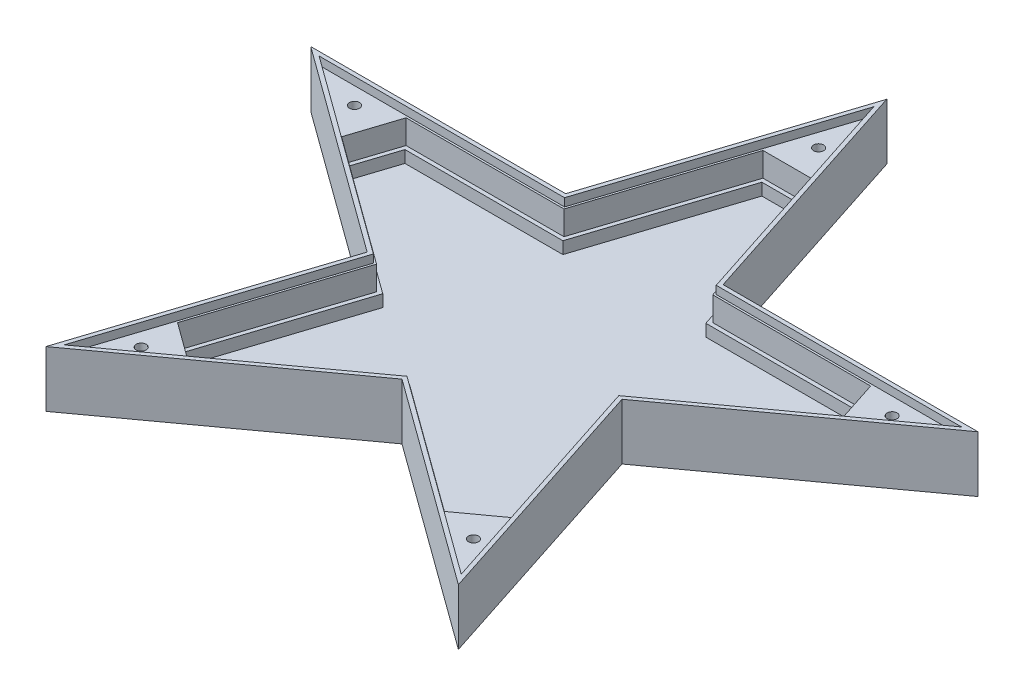
SolidWorks part; units mm, degrees
ref_plane "Alzado" through (0, 0, 0) normal (0, 0, 1) x (1, 0, 0)
ref_plane "Planta" through (0, 0, 0) normal (0, 1, 0) x (1, 0, 0)
ref_plane "Vista lateral" through (0, 0, 0) normal (1, 0, 0) x (0, 0, -1)
sketch "Croquis1" plane through (0, 0, 0) normal (0, 1, 0) x (1, 0, 0)
  line L0 (0, 0) -> (0, 87.5) construction
  line L1 (0, 87.5) -> (-19.645, 27.039)
  line L2 (-19.645, 27.039) -> (-83.2174, 27.039)
  line L3 (-83.2174, 27.039) -> (-31.7862, -10.328)
  line L4 (-31.7862, -10.328) -> (-51.4312, -70.789)
  line L5 (-51.4312, -70.789) -> (0, -33.422)
  line L6 (0, 87.5) -> (-51.4312, -70.789) construction
  line L7 (0, -33.422) -> (0, 0) construction
  line L8 (0, 87.5) -> (19.645, 27.039)
  line L9 (19.645, 27.039) -> (83.2174, 27.039)
  line L10 (83.2174, 27.039) -> (31.7862, -10.328)
  line L11 (31.7862, -10.328) -> (51.4312, -70.789)
  line L12 (51.4312, -70.789) -> (0, -33.422)
  line L14 (0, 87.5) -> (0, 0) construction
  line L15 (0, 0) -> (-83.2174, 27.039) construction
  line L16 (0, 0) -> (83.2174, 27.039) construction
  line L17 (51.4312, -70.789) -> (0, 0) construction
  line L18 (0, 0) -> (-51.4312, -70.789) construction
  line L19 (-55.5183, 23.2963) -> (-7.9655, 7.8455) construction
  line L20 (-7.9655, 7.8455) -> (-11.0557, -1.6651) construction
  line L21 (-11.0557, -1.6651) -> (-58.6085, 13.7857) construction
  line L22 (-58.6085, 13.7857) -> (-55.5183, 23.2963) construction
  line L23 (-39.3122, -45.6021) -> (-9.9229, -5.1512) construction
  line L24 (-9.9229, -5.1512) -> (-1.8328, -11.0291) construction
  line L25 (-1.8328, -11.0291) -> (-31.222, -51.4799) construction
  line L26 (-31.222, -51.4799) -> (-39.3122, -45.6021) construction
  line L27 (-17.8286, 24.539) -> (-75.5232, 24.539) construction
  line L28 (-75.5232, 24.539) -> (-28.8473, -9.3731) construction
  line L29 (-28.8473, -9.3731) -> (-46.6759, -64.2439) construction
  line L30 (-46.6759, -64.2439) -> (0, -30.3319) construction
  line L31 (46.6759, -64.2439) -> (0, -30.3319) construction
  line L32 (28.8473, -9.3731) -> (46.6759, -64.2439) construction
  line L33 (75.5232, 24.539) -> (28.8473, -9.3731) construction
  line L34 (17.8286, 24.539) -> (75.5232, 24.539) construction
  line L35 (0, 79.4098) -> (17.8286, 24.539) construction
  line L36 (0, 79.4098) -> (-17.8286, 24.539) construction
  line L37 (51.4312, -70.789) -> (83.2174, 27.039) construction
  line L38 (0, 87.5) -> (83.2174, 27.039) construction
  line L39 (0, 87.5) -> (-83.2174, 27.039) construction
  line L40 (-83.2174, 27.039) -> (-51.4312, -70.789) construction
  line L41 (-51.4312, -70.789) -> (51.4312, -70.789) construction
  line L42 (5, 60) -> (5, 10) construction
  line L43 (5, 10) -> (-5, 10) construction
  line L44 (-5, 10) -> (-5, 60) construction
  line L45 (-5, 60) -> (5, 60) construction
  line L46 (58.6085, 13.7857) -> (55.5183, 23.2963) construction
  line L47 (55.5183, 23.2963) -> (7.9655, 7.8455) construction
  line L48 (7.9655, 7.8455) -> (11.0557, -1.6651) construction
  line L49 (11.0557, -1.6651) -> (58.6085, 13.7857) construction
  line L50 (31.222, -51.4799) -> (39.3122, -45.6021) construction
  line L51 (39.3122, -45.6021) -> (9.9229, -5.1512) construction
  line L52 (9.9229, -5.1512) -> (1.8328, -11.0291) construction
  line L53 (1.8328, -11.0291) -> (31.222, -51.4799) construction
  circle A0 centre (0, 0) radius 87.5 construction
  circle A1 centre (0, 0) radius 10 construction
  circle A2 centre (0, 0) radius 7.5 construction
  point P15 (-9.5106, 3.0902)
  point P20 (-5.8779, -8.0902)
  point P39 (0, 60)
  dimension "D1" = 175
  dimension "D5" = 20
  dimension "D6" = 15
  dimension "D2" = 50
  dimension "D3" = 10
  dimension "D4" = 2.5
extrude "Saliente-Extruir1" add sketch "Croquis1" along normal blind 14
sketch "Croquis2" plane through (0, 14, 0) normal (0, 1, 0) x (1, 0, 0)
  line L0 (0, -96.25) -> (0, 96.25) construction
  line L1 (31.8662, -53.484) -> (41.0191, -46.8341)
  line L2 (60.7136, 13.7791) -> (57.2175, 24.539)
  line L10 (-60.7136, 13.7791) -> (-57.2175, 24.539)
  line L11 (-58.6085, 13.7857) -> (-55.5183, 23.2963) construction
  line L12 (-31.8662, -53.484) -> (-41.0191, -46.8341)
  line L13 (-5.6568, 62) -> (5.6568, 62)
  line L14 (-5, 60) -> (5, 60) construction
  line L15 (-31.222, -51.4799) -> (-39.3122, -45.6021) construction
  line L16 (-55.5183, 23.2963) -> (-57.4204, 23.9143) construction
  line L17 (-31.222, -51.4799) -> (-32.3976, -53.098) construction
  line L18 (5, 60) -> (5, 62) construction
  line L20 (17.8286, 24.539) -> (0, 79.4098)
  line L21 (0, 79.4098) -> (-17.8286, 24.539)
  line L22 (-17.8286, 24.539) -> (-75.5232, 24.539)
  line L23 (-75.5232, 24.539) -> (-28.8473, -9.3731)
  line L24 (-28.8473, -9.3731) -> (-46.6759, -64.2439)
  line L25 (-46.6759, -64.2439) -> (0, -30.3319)
  line L26 (0, -30.3319) -> (46.6759, -64.2439)
  line L27 (46.6759, -64.2439) -> (28.8473, -9.3731)
  line L28 (28.8473, -9.3731) -> (75.5232, 24.539)
  line L29 (75.5232, 24.539) -> (17.8286, 24.539)
  line L30 (17.8286, 24.539) -> (5.6568, 62)
  line L31 (-5.6568, 62) -> (-17.8286, 24.539)
  line L32 (-17.8286, 24.539) -> (-57.2175, 24.539)
  line L33 (-60.7136, 13.7791) -> (-28.8473, -9.3731)
  line L34 (-28.8473, -9.3731) -> (-41.0191, -46.8341)
  line L35 (-31.8662, -53.484) -> (0, -30.3319)
  line L36 (0, -30.3319) -> (31.8662, -53.484)
  line L37 (41.0191, -46.8341) -> (28.8473, -9.3731)
  line L38 (28.8473, -9.3731) -> (60.7136, 13.7791)
  line L39 (57.2175, 24.539) -> (17.8286, 24.539)
  dimension "D2" = 2
  dimension "D1" = 2.5
extrude "Cortar-Extruir1" cut sketch "Croquis2" against normal blind 11
sketch "Croquis3" plane through (0, 14, 0) normal (0, 1, 0) x (1, 0, 0)
  line L27 (57.2175, 24.539) -> (17.8286, 24.539)
  line L28 (17.8286, 24.539) -> (5.6568, 62)
  line L29 (-5.6568, 62) -> (-17.8286, 24.539)
  line L30 (-17.8286, 24.539) -> (-57.2175, 24.539)
  line L31 (-60.7136, 13.7791) -> (-28.8473, -9.3731)
  line L32 (-28.8473, -9.3731) -> (-41.0191, -46.8341)
  line L33 (-31.8662, -53.484) -> (0, -30.3319)
  line L34 (0, -30.3319) -> (31.8662, -53.484)
  line L35 (41.0191, -46.8341) -> (28.8473, -9.3731)
  line L36 (28.8473, -9.3731) -> (60.7136, 13.7791)
  line L37 (57.2175, 24.539) -> (17.8286, 24.539)
  line L38 (17.8286, 24.539) -> (5.6568, 62)
  line L39 (-5.6568, 62) -> (-17.8286, 24.539)
  line L40 (-17.8286, 24.539) -> (-57.2175, 24.539)
  line L41 (-60.7136, 13.7791) -> (-28.8473, -9.3731)
  line L42 (-28.8473, -9.3731) -> (-41.0191, -46.8341)
  line L43 (-31.8662, -53.484) -> (0, -30.3319)
  line L44 (0, -30.3319) -> (31.8662, -53.484)
  line L45 (41.0191, -46.8341) -> (28.8473, -9.3731)
  line L46 (28.8473, -9.3731) -> (60.7136, 13.7791)
  line L57 (57.944, 25.539) -> (18.5552, 25.539)
  line L58 (18.5552, 25.539) -> (6.3833, 63)
  line L59 (-6.3833, 63) -> (-18.5552, 25.539)
  line L60 (-18.5552, 25.539) -> (-57.944, 25.539)
  line L61 (-61.8891, 13.3972) -> (-30.0229, -9.755)
  line L62 (-30.0229, -9.755) -> (-42.1947, -47.216)
  line L63 (-31.8662, -54.7201) -> (0, -31.5679)
  line L64 (0, -31.5679) -> (31.8662, -54.7201)
  line L65 (42.1947, -47.216) -> (30.0229, -9.755)
  line L66 (30.0229, -9.755) -> (61.8891, 13.3972)
  line L67 (57.944, 25.539) -> (18.5552, 25.539)
  line L68 (18.5552, 25.539) -> (6.3833, 63)
  line L69 (-6.3833, 63) -> (-18.5552, 25.539)
  line L70 (-18.5552, 25.539) -> (-57.944, 25.539)
  line L71 (-61.8891, 13.3972) -> (-30.0229, -9.755)
  line L72 (-30.0229, -9.755) -> (-42.1947, -47.216)
  line L73 (-31.8662, -54.7201) -> (0, -31.5679)
  line L74 (0, -31.5679) -> (31.8662, -54.7201)
  line L75 (42.1947, -47.216) -> (30.0229, -9.755)
  line L76 (30.0229, -9.755) -> (61.8891, 13.3972)
  line L82 (-41.0191, -46.8341) -> (-31.8662, -53.484)
  line L83 (-41.0191, -46.8341) -> (-31.8662, -53.484)
  line L84 (31.8662, -53.484) -> (41.0191, -46.8341)
  line L85 (31.8662, -53.484) -> (41.0191, -46.8341)
  line L86 (60.7136, 13.7791) -> (57.2175, 24.539)
  line L87 (60.7136, 13.7791) -> (57.2175, 24.539)
  line L88 (5.6568, 62) -> (-5.6568, 62)
  line L89 (5.6568, 62) -> (-5.6568, 62)
  line L90 (-57.2175, 24.539) -> (-60.7136, 13.7791)
  line L91 (-57.2175, 24.539) -> (-60.7136, 13.7791)
  line L92 (-42.1947, -47.216) -> (-31.8662, -54.7201)
  line L93 (-42.1947, -47.216) -> (-31.8662, -54.7201)
  line L94 (31.8662, -54.7201) -> (42.1947, -47.216)
  line L95 (31.8662, -54.7201) -> (42.1947, -47.216)
  line L96 (61.8891, 13.3972) -> (57.944, 25.539)
  line L97 (61.8891, 13.3972) -> (57.944, 25.539)
  line L98 (6.3833, 63) -> (-6.3833, 63)
  line L99 (6.3833, 63) -> (-6.3833, 63)
  line L100 (-57.944, 25.539) -> (-61.8891, 13.3972)
  line L101 (-57.944, 25.539) -> (-61.8891, 13.3972)
  dimension "D1" = 0
  dimension "D2" = 1
extrude "Cortar-Extruir2" cut sketch "Croquis3" against normal blind 8
sketch "Croquis4" plane through (0, 14, 0) normal (0, 1, 0) x (1, 0, 0)
  line L31 (18.9184, 26.039) -> (0, 84.2639)
  line L32 (0, 84.2639) -> (-18.9184, 26.039)
  line L33 (-18.9184, 26.039) -> (-80.1398, 26.039)
  line L34 (-80.1398, 26.039) -> (-30.6107, -9.946)
  line L35 (-30.6107, -9.946) -> (-49.5291, -68.171)
  line L36 (-49.5291, -68.171) -> (0, -32.186)
  line L37 (0, -32.186) -> (49.5291, -68.171)
  line L38 (49.5291, -68.171) -> (30.6107, -9.946)
  line L39 (30.6107, -9.946) -> (80.1398, 26.039)
  line L40 (80.1398, 26.039) -> (18.9184, 26.039)
  line L41 (19.645, 27.039) -> (0, 87.5)
  line L42 (0, 87.5) -> (-19.645, 27.039)
  line L43 (-19.645, 27.039) -> (-83.2174, 27.039)
  line L44 (-83.2174, 27.039) -> (-31.7862, -10.328)
  line L45 (-31.7862, -10.328) -> (-51.4312, -70.789)
  line L46 (-51.4312, -70.789) -> (0, -33.422)
  line L47 (0, -33.422) -> (51.4312, -70.789)
  line L48 (51.4312, -70.789) -> (31.7862, -10.328)
  line L49 (31.7862, -10.328) -> (83.2174, 27.039)
  line L50 (83.2174, 27.039) -> (19.645, 27.039)
  line L51 (19.645, 27.039) -> (0, 87.5)
  line L52 (0, 87.5) -> (-19.645, 27.039)
  line L53 (-19.645, 27.039) -> (-83.2174, 27.039)
  line L54 (-83.2174, 27.039) -> (-31.7862, -10.328)
  line L55 (-31.7862, -10.328) -> (-51.4312, -70.789)
  line L56 (-51.4312, -70.789) -> (0, -33.422)
  line L57 (0, -33.422) -> (51.4312, -70.789)
  line L58 (51.4312, -70.789) -> (31.7862, -10.328)
  line L59 (31.7862, -10.328) -> (83.2174, 27.039)
  line L60 (83.2174, 27.039) -> (19.645, 27.039)
  dimension "D1" = 0
  dimension "D2" = 1
extrude "Cortar-Extruir4" cut sketch "Croquis4" against normal blind 2 flip side to cut
sketch "Croquis6" plane through (0, 12, 0) normal (0, 1, 0) x (1, 0, 0)
  line L0 (0, 0) -> (-83.2174, 27.039) construction
  line L2 (0, 0) -> (0, 87.5) construction
  line L3 (0, -7.7) -> (0, 7.7) construction
  line L4 (51.4312, -70.789) -> (0, 0) construction
  circle A0 centre (-67.0495, 21.7857) radius 1.25
  circle A2 centre (0, 70.5) radius 1.25
  circle A3 centre (67.0495, 21.7857) radius 1.25
  circle A4 centre (41.4389, -57.0357) radius 1.25
  circle A5 centre (-41.4389, -57.0357) radius 1.25
  dimension "D1" = 2.5
  dimension "D4" = 17
  dimension "D2" = 17
  dimension "D3" = 17
extrude "Cortar-Extruir6" cut sketch "Croquis6" against normal blind 7
equation "\"D1@Saliente-Extruir1\"=2+4+3+2+3"
